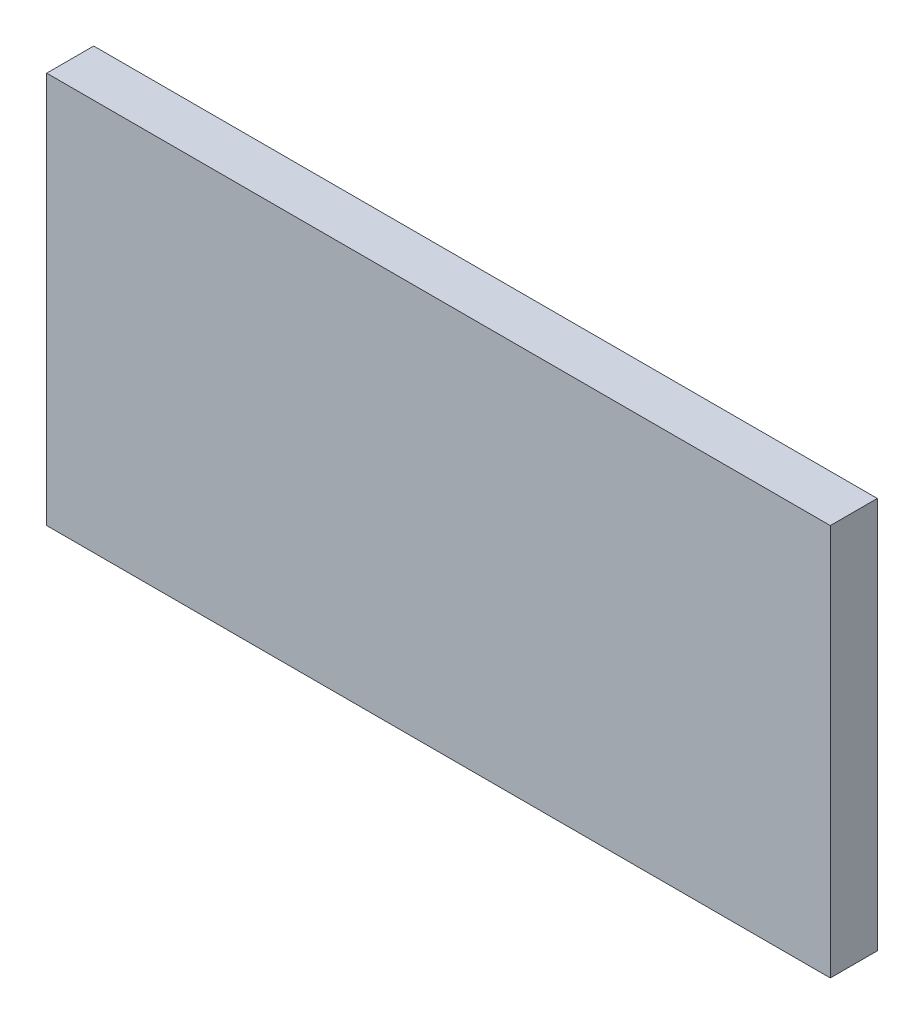
SolidWorks part; units mm, degrees
ref_plane "Front Plane" through (0, 0, 0) normal (0, 0, 1) x (1, 0, 0)
ref_plane "Top Plane" through (0, 0, 0) normal (0, 1, 0) x (1, 0, 0)
ref_plane "Right Plane" through (0, 0, 0) normal (1, 0, 0) x (0, 0, -1)
sketch "Sketch1" plane through (0, 0, 0) normal (0, 0, 1) x (1, 0, 0)
  line L1 (-4.3249, 48.2173) -> (95.6751, 48.2173)
  line L2 (-4.3249, 48.2173) -> (-4.3249, -1.7827)
  line L3 (-4.3249, -1.7827) -> (95.6751, -1.7827)
  line L4 (95.6751, 48.2173) -> (95.6751, -1.7827)
  dimension "D1" = 50
  dimension "D2" = 100
extrude "Boss-Extrude1" add sketch "Sketch1" along normal blind 6
